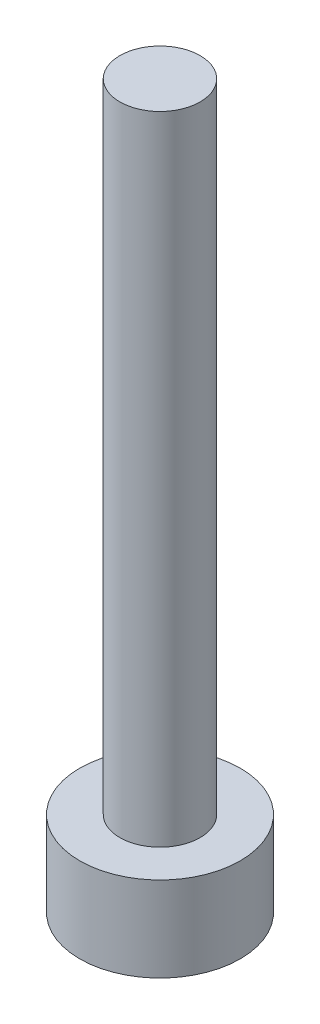
SolidWorks part; units mm, degrees
ref_plane "Front Plane" through (0, 0, 0) normal (0, 0, 1) x (1, 0, 0)
ref_plane "Top Plane" through (0, 0, 0) normal (0, 1, 0) x (1, 0, 0)
ref_plane "Right Plane" through (0, 0, 0) normal (1, 0, 0) x (0, 0, -1)
sketch "Sketch1" plane through (0, 0, 0) normal (0, 0, 1) x (1, 0, 0)
  line L1 (0, 0) -> (-6, 0)
  line L2 (0, 0) -> (0, 6.35)
  line L3 (0, 6.35) -> (-6, 6.35)
  line L4 (-6, 0) -> (-6, 6.35)
  line L6 (0, 6.35) -> (0, 53.975)
  line L7 (0, 53.975) -> (-3, 53.975)
  line L8 (-3, 6.35) -> (-3, 53.975)
  point P8 (0, 0)
  dimension "D1" = 3
  dimension "D2" = 6
  dimension "D3" = 6.35
  dimension "D4" = 47.625
revolve "Revolve1" add sketch "Sketch1" angle 360 about L6
